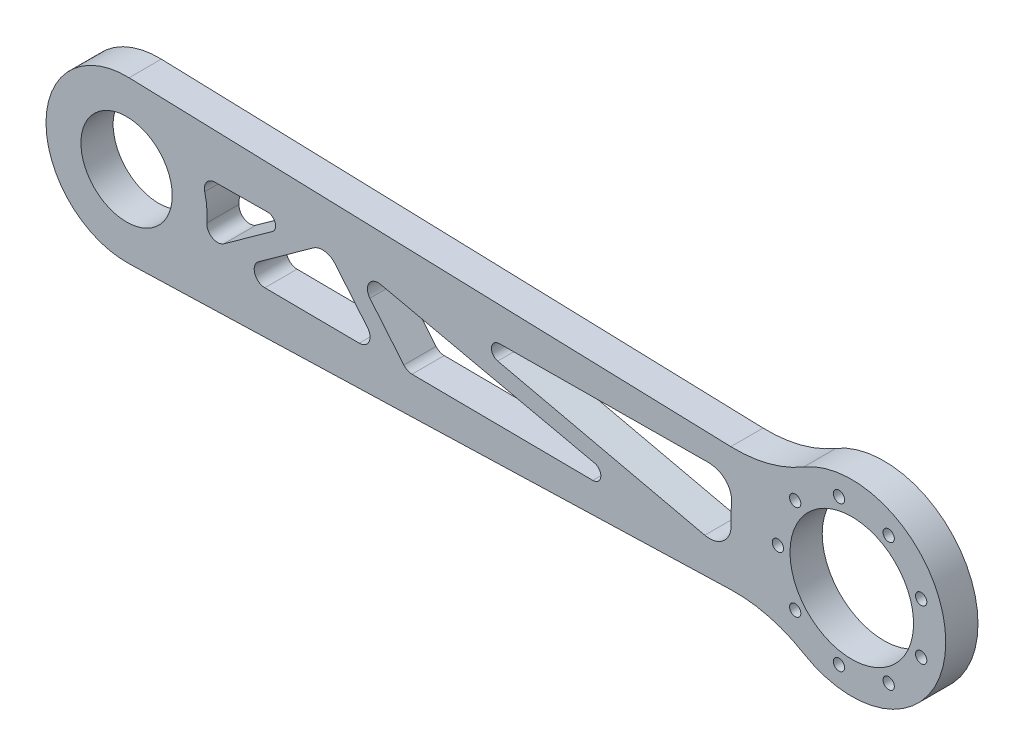
SolidWorks part; units mm, degrees
material "Thornel Mat VMA"
ref_plane "前视基准面" through (0, 0, 0) normal (0, 0, 1) x (1, 0, 0)
ref_plane "上视基准面" through (0, 0, 0) normal (0, 1, 0) x (1, 0, 0)
ref_plane "右视基准面" through (0, 0, 0) normal (1, 0, 0) x (0, 0, -1)
sketch "草图1" plane through (0, 0, 0) normal (0, 0, 1) x (1, 0, 0)
  line L0 (0.9265, 29.9857) -> (243.1905, 22.5)
  line L1 (0.9265, -29.9857) -> (243.1905, -22.5)
  line L2 (0, 0) -> (270, 0) construction
  arc A0 (0.9265, 29.9857) -> (0.9265, -29.9857) centre (0, 0) ccw
  arc A1 (243.1905, -22.5) -> (243.1905, 22.5) centre (270, 0) ccw
  dimension "D1" = 60
  dimension "D2" = 70
  dimension "D3" = 270
  dimension "D4" = 45
extrude "凸台-拉伸1" add sketch "草图1" along normal blind 12
sketch "草图2" plane through (0, 0, 12) normal (0, 0, 1) x (1, 0, 0)
  circle A0 centre (0, 0) radius 17
  dimension "D1" = 34
extrude "切除-拉伸1" cut sketch "草图2" against normal through all
sketch "草图3" plane through (0, 0, 12) normal (0, 0, 1) x (1, 0, 0)
  circle A0 centre (0, 0) radius 19 construction
  circle A1 centre (-19, 0) radius 1.6
  circle A2 centre (-9.5, 16.4545) radius 1.6
  circle A3 centre (9.5, 16.4545) radius 1.6
  circle A4 centre (19, 0) radius 1.6
  circle A5 centre (9.5, -16.4545) radius 1.6
  circle A6 centre (-9.5, -16.4545) radius 1.6
  dimension "D1" = 38
  dimension "D2" = 3.2
  dimension "D3" = 6
extrude "切除-拉伸2" [suppressed] cut sketch "草图3" against normal through all
fillet "圆角1" radius 50 2 edges at (243.1905, -22.5, 6) (243.1905, 22.5, 6)
sketch "草图6" plane through (0, 0, 0) normal (0, 0, -1) x (-1, 0, 0)
  circle A0 centre (-270, 0) radius 27.5 construction
  circle A1 centre (-242.5, 0) radius 2.1
  circle A2 centre (-248.9338, -17.6767) radius 2.1
  circle A3 centre (-265.2247, -27.0822) radius 2.1
  circle A4 centre (-283.75, -23.8157) radius 2.1
  circle A5 centre (-295.8415, -9.4056) radius 2.1
  circle A6 centre (-295.8415, 9.4056) radius 2.1
  circle A7 centre (-283.75, 23.8157) radius 2.1
  circle A8 centre (-265.2247, 27.0822) radius 2.1
  circle A9 centre (-248.9338, 17.6767) radius 2.1
  dimension "D1" = 55
  dimension "D2" = 4.2
  dimension "D3" = 9
extrude "切除-拉伸5" cut sketch "草图6" against normal through all
sketch "草图7" plane through (0, 0, 12) normal (0, 0, 1) x (1, 0, 0)
  circle A21 centre (0, 0) radius 17 construction
  arc A22 (-3.4814, -16.6397) -> (3.4814, -16.6397) centre (0, 0) ccw
  arc A23 (3.4814, -16.6397) -> (-3.4814, -16.6397) centre (0, -17) ccw
  arc A24 (-14.7495, -8.453) -> (-16.9011, -1.8309) centre (-16.168, -5.2533) ccw
  arc A25 (-12.5971, 11.4155) -> (-6.9641, 15.5081) centre (-9.9923, 13.7533) ccw
  arc A26 (6.9641, 15.5081) -> (12.5971, 11.4155) centre (9.9923, 13.7533) ccw
  arc A27 (16.9011, -1.8309) -> (14.7495, -8.453) centre (16.168, -5.2533) ccw
  arc A28 (-16.9011, -1.8309) -> (-14.7495, -8.453) centre (0, 0) ccw
  arc A29 (-6.9641, 15.5081) -> (-12.5971, 11.4155) centre (0, 0) ccw
  arc A30 (12.5971, 11.4155) -> (6.9641, 15.5081) centre (0, 0) ccw
  arc A31 (14.7495, -8.453) -> (16.9011, -1.8309) centre (0, 0) ccw
  dimension "D1" = 7
extrude "凸台-拉伸3" [suppressed] add sketch "草图7" against normal up to surface (15 mm away)
fillet "圆角2" [suppressed] radius 2
sketch "草图8" plane through (0, 0, 0) normal (0, 0, -1) x (-1, 0, 0)
  circle A0 centre (-270, 0) radius 23
  dimension "D1" = 46
extrude "切除-拉伸6" cut sketch "草图8" against normal through all
sketch "草图9" plane through (0, 0, 12) normal (0, 0, 1) x (1, 0, 0)
  line L1 (138.1772, 7.266) -> (215.28, -10.3405)
  line L2 (32.9375, 12.2958) -> (52.4452, 12.4661)
  line L3 (54.2216, 7.0297) -> (36.2306, -5.894)
  line L4 (51.4811, -12.4577) -> (86.6171, -12.7643)
  line L5 (89.7281, -6.2076) -> (77.6242, 8.3549)
  line L6 (69.5095, 9.3927) -> (49.1824, -5.2091)
  line L7 (103.2233, -11.4927) -> (90.5775, 3.7216)
  line L8 (94.5244, 10.1825) -> (174.2302, -7.595)
  line L9 (173.5509, -13.5229) -> (106.2645, -12.9357)
  line L10 (0.9265, -29.9857) -> (224.978, -23.0627) construction
  line L11 (226.9181, -12.998) -> (201.9181, -13.7705) construction
  line L12 (394.8153, -15.4539) -> (-27.6151, -11.7674) construction
  line L13 (270, 0) -> (-38.053, 0) construction
  line L14 (394.8153, 15.4539) -> (-27.6151, 11.7674) construction
  line L19 (217.0921, 13.7846) -> (138.8223, 13.1906)
  arc A0 (225.0518, -2.1576) -> (225.2579, 4.8113) centre (270, 0) cw
  arc A1 (29.0933, 7.32) -> (29.9091, -2.3341) centre (0, 0) cw
  arc A3 (225.0518, -2.1576) -> (215.28, -10.3405) centre (217.061, -2.5412) cw
  arc A4 (224.6691, 13.0675) -> (257.2124, 21.482) centre (226.5222, 73.0389) ccw
  arc A5 (217.0921, 13.7846) -> (218.3883, 13.5928) centre (226.5222, 73.0389) ccw
  arc A6 (225.2579, 4.8113) -> (218.3883, 13.5928) centre (217.3038, 5.6666) ccw
  arc A7 (174.2302, -7.595) -> (173.5509, -13.5229) centre (173.5771, -10.5231) cw
  arc A8 (138.1772, 7.266) -> (138.8223, 13.1906) centre (138.8451, 10.1907) cw
  arc A9 (90.5775, 3.7216) -> (94.5244, 10.1825) centre (93.6537, 6.2784) cw
  arc A10 (77.6242, 8.3549) -> (69.5095, 9.3927) centre (73.01, 4.5197) ccw
  arc A11 (52.4452, 12.4661) -> (54.2216, 7.0297) centre (52.4714, 9.4662) cw
  arc A12 (29.0933, 7.32) -> (32.9375, 12.2958) centre (32.9724, 8.296) cw
  arc A13 (29.9091, -2.3341) -> (36.2306, -5.894) centre (33.8969, -2.6454) ccw
  arc A14 (103.2233, -11.4927) -> (106.2645, -12.9357) centre (106.2994, -8.9359) ccw
  arc A15 (86.6171, -12.7643) -> (89.7281, -6.2076) centre (86.652, -8.7644) ccw
  arc A16 (51.4811, -12.4577) -> (49.1824, -5.2091) centre (51.516, -8.4578) cw
  point P41 (113.0871, 12.9953)
  point P44 (83.0871, 12.7335)
  point P47 (74.0504, 12.6546)
  point P50 (61.9045, 12.5486)
  point P53 (27.3862, 12.2474)
  point P57 (27.3862, -12.2474)
  point P62 (95.2404, -12.8395)
  point P65 (39.2404, -12.3508)
  dimension "D1" = 45
  dimension "D11" = 30
  dimension "D10" = 8
  dimension "D12" = 3
  dimension "D13" = 3
  dimension "D15" = 4
  dimension "D16" = 6
  dimension "D17" = 3
  dimension "D18" = 4
  dimension "D19" = 4
  dimension "D20" = 4
  dimension "D21" = 4
  dimension "D2" = 10
  dimension "D3" = 0.5
  dimension "D4" = 30
  dimension "D5" = 7
  dimension "D6" = 7
  dimension "D7" = 25
  dimension "D8" = 10
  dimension "D9" = 34.5184
  dimension "D14" = 56
extrude "切除-拉伸7" cut sketch "草图9" against normal through all
sketch "草图10" plane through (0, 0, 12) normal (0, 0, 1) x (1, 0, 0)
  line L0 (272.6477, 34.8997) -> (302.8376, 12.1116)
  arc A0 (252.0974, -30.0748) -> (252.0974, 30.0748) centre (270, 0) ccw construction
  arc A1 (302.8376, 12.1116) -> (272.6477, 34.8997) centre (270, 0) ccw
extrude "切除-拉伸8" [suppressed] cut sketch "草图10" against normal through all
sketch "草图11" plane through (0, 0, 12) normal (0, 0, 1) x (1, 0, 0)
  circle A0 centre (270, 0) radius 35.5
  dimension "D1" = 71
extrude "切除-拉伸9" [suppressed] cut sketch "草图11" against normal blind 3
sketch "草图12" plane through (0, 0, 0) normal (1, 0, 0) x (0, 0, -1)
  line L1 (0, 0) -> (2.6273, 0)
  line L2 (0, 0) -> (0, 4.213)
  line L3 (0, 4.213) -> (2.6273, 4.213)
  line L4 (2.6273, 0) -> (2.6273, 4.213)
extrude "凸台-拉伸4" add sketch "草图12" along normal blind 2 separate body
sketch "草图13" plane through (0, 0, 0) normal (1, 0, 0) x (0, 0, -1)
  circle A0 centre (-9.7975, 0) radius 2.5668
extrude "凸台-拉伸5" add sketch "草图13" along normal blind 2 separate body
chamfer "倒角1" [suppressed] distance 2.5 angle 45
sketch "草图14" [suppressed] plane through (0, 0, 9) normal (0, 0, 1) x (1, 0, 0)
  line L0 (270, 0) -> (209.5497, 0) construction
  line L1 (238.7424, 6.3413) -> (245.5689, 3.7907)
  line L2 (238.7424, -6.3413) -> (245.5689, -3.7907)
  line L3 (242.4138, 17.371) -> (249.8484, 13.8804)
  line L4 (250.7439, 26.3525) -> (254.8342, 19.2678)
  line L5 (256.8061, 29.8525) -> (260.8964, 22.7678)
  line L6 (279.5957, 22.6202) -> (283.6711, 29.6791)
  line L7 (284.7918, 19.6202) -> (288.8673, 26.6791)
  line L8 (294, 4.5) -> (302.249, 4.5)
  line L9 (256.8061, -29.8525) -> (260.8964, -22.7678)
  line L10 (279.5957, -22.6202) -> (283.6711, -29.6791)
  line L11 (284.7918, -19.6202) -> (288.8673, -26.6791)
  line L12 (294, -4.5) -> (302.249, -4.5)
  line L13 (250.7439, -26.3525) -> (254.8342, -19.2678)
  line L14 (242.4138, -17.371) -> (249.8484, -13.8804)
  arc A0 (247.5166, 0.8651) -> (247.5166, -0.8651) centre (270, 0) ccw
  circle A1 centre (270, 0) radius 35.5 construction
  arc A2 (234.7101, 3.8569) -> (234.7101, -3.8569) centre (270, 0) ccw
  circle A3 centre (230, 0) radius 2.1 construction
  circle A4 centre (250, 34.641) radius 2.1 construction
  arc A5 (254.4023, 16.2161) -> (252.8198, 14.529) centre (270, 0) ccw
  arc A6 (246.9561, 27.0042) -> (241.4669, 21.1214) centre (270, 0) ccw
  circle A7 centre (290, 34.641) radius 2.1 construction
  arc A8 (276.6875, 21.4832) -> (263.7553, 21.6161) centre (270, 0) ccw
  arc A9 (282.3778, 33.2722) -> (258.1357, 33.4587) centre (270, 0) ccw
  circle A10 centre (310, 0) radius 2.1 construction
  arc A11 (304.6921, 7.5303) -> (292.6257, 27.3556) centre (270, 0) ccw
  arc A12 (291.6, 6.3) -> (285.2612, 16.5332) centre (270, 0) ccw
  arc A13 (302.249, 4.5) -> (304.6921, 7.5303) centre (302.249, 7) ccw
  arc A14 (291.6, 6.3) -> (294, 4.5) centre (294, 7) ccw
  arc A15 (279.5957, 22.6202) -> (276.6875, 21.4832) centre (277.4306, 23.8702) cw
  arc A16 (283.6711, 29.6791) -> (282.3778, 33.2722) centre (281.5061, 30.9291) ccw
  arc A17 (288.8673, 26.6791) -> (292.6257, 27.3556) centre (291.0324, 25.4291) cw
  arc A18 (284.7918, 19.6202) -> (285.2612, 16.5332) centre (286.9569, 18.3702) ccw
  arc A19 (250.7439, 26.3525) -> (246.9561, 27.0042) centre (248.5789, 25.1025) ccw
  arc A20 (254.8342, 19.2678) -> (254.4023, 16.2161) centre (252.6692, 18.0178) cw
  arc A21 (249.8484, 13.8804) -> (252.8198, 14.529) centre (250.9109, 16.1433) ccw
  arc A22 (242.4138, 17.371) -> (241.4669, 21.1214) centre (243.4763, 19.634) cw
  arc A23 (256.8061, 29.8525) -> (258.1357, 33.4587) centre (258.9712, 31.1025) cw
  arc A24 (260.8964, 22.7678) -> (263.7553, 21.6161) centre (263.0615, 24.0178) ccw
  arc A25 (245.5689, -3.7907) -> (247.5166, -0.8651) centre (244.5189, -0.9804) ccw
  arc A26 (238.7424, -6.3413) -> (234.7101, -3.8569) centre (237.6924, -3.531) cw
  arc A27 (238.7424, 6.3413) -> (234.7101, 3.8569) centre (237.6924, 3.531) ccw
  arc A28 (245.5689, 3.7907) -> (247.5166, 0.8651) centre (244.5189, 0.9804) cw
  arc A29 (276.6875, -21.4832) -> (263.7553, -21.6161) centre (270, 0) cw
  arc A30 (260.8964, -22.7678) -> (263.7553, -21.6161) centre (263.0615, -24.0178) cw
  arc A31 (256.8061, -29.8525) -> (258.1357, -33.4587) centre (258.9712, -31.1025) ccw
  arc A32 (282.3778, -33.2722) -> (258.1357, -33.4587) centre (270, 0) cw
  arc A33 (279.5957, -22.6202) -> (276.6875, -21.4832) centre (277.4306, -23.8702) ccw
  arc A34 (283.6711, -29.6791) -> (282.3778, -33.2722) centre (281.5061, -30.9291) cw
  arc A35 (291.6, -6.3) -> (285.2612, -16.5332) centre (270, 0) cw
  arc A36 (284.7918, -19.6202) -> (285.2612, -16.5332) centre (286.9569, -18.3702) cw
  arc A37 (288.8673, -26.6791) -> (292.6257, -27.3556) centre (291.0324, -25.4291) ccw
  arc A38 (304.6921, -7.5303) -> (292.6257, -27.3556) centre (270, 0) cw
  arc A39 (302.249, -4.5) -> (304.6921, -7.5303) centre (302.249, -7) cw
  arc A40 (291.6, -6.3) -> (294, -4.5) centre (294, -7) cw
  arc A41 (246.9561, -27.0042) -> (241.4669, -21.1214) centre (270, 0) cw
  arc A42 (250.7439, -26.3525) -> (246.9561, -27.0042) centre (248.5789, -25.1025) cw
  arc A43 (254.8342, -19.2678) -> (254.4023, -16.2161) centre (252.6692, -18.0178) ccw
  arc A44 (254.4023, -16.2161) -> (252.8198, -14.529) centre (270, 0) cw
  arc A45 (249.8484, -13.8804) -> (252.8198, -14.529) centre (250.9109, -16.1433) cw
  arc A46 (242.4138, -17.371) -> (241.4669, -21.1214) centre (243.4763, -19.634) ccw
  point P32 (305.2136, 4.5)
  point P37 (278.5515, 20.8116)
  point P40 (285.0884, 32.1339)
  point P47 (249.3054, 28.8441)
  point P50 (255.8559, 17.4984)
  point P61 (247.7001, -2.9943)
  point P64 (235.3269, -7.6174)
  point P67 (235.3269, 7.6174)
  point P70 (247.7001, 2.9943)
  dimension "D1" = 45
  dimension "D4" = 3.5
  dimension "D8" = 3.5
  dimension "D13" = 3
  dimension "D15" = 2.5
  dimension "D16" = 3
  dimension "D2" = 9
  dimension "D3" = 21
  dimension "D5" = 3.5
  dimension "D6" = 4
  dimension "D7" = 5
  dimension "D9" = 3.5
  dimension "D10" = 3
  dimension "D11" = 3
  dimension "D12" = 3
  dimension "D14" = 4.5
extrude "切除-拉伸10" [suppressed] cut sketch "草图14" against normal through all
delete or keep bodies "实体-删除/保留 1" type delete bodies bodies 119 118
move or copy body "实体-移动/复制1" [suppressed] bodies to move or copy 115
